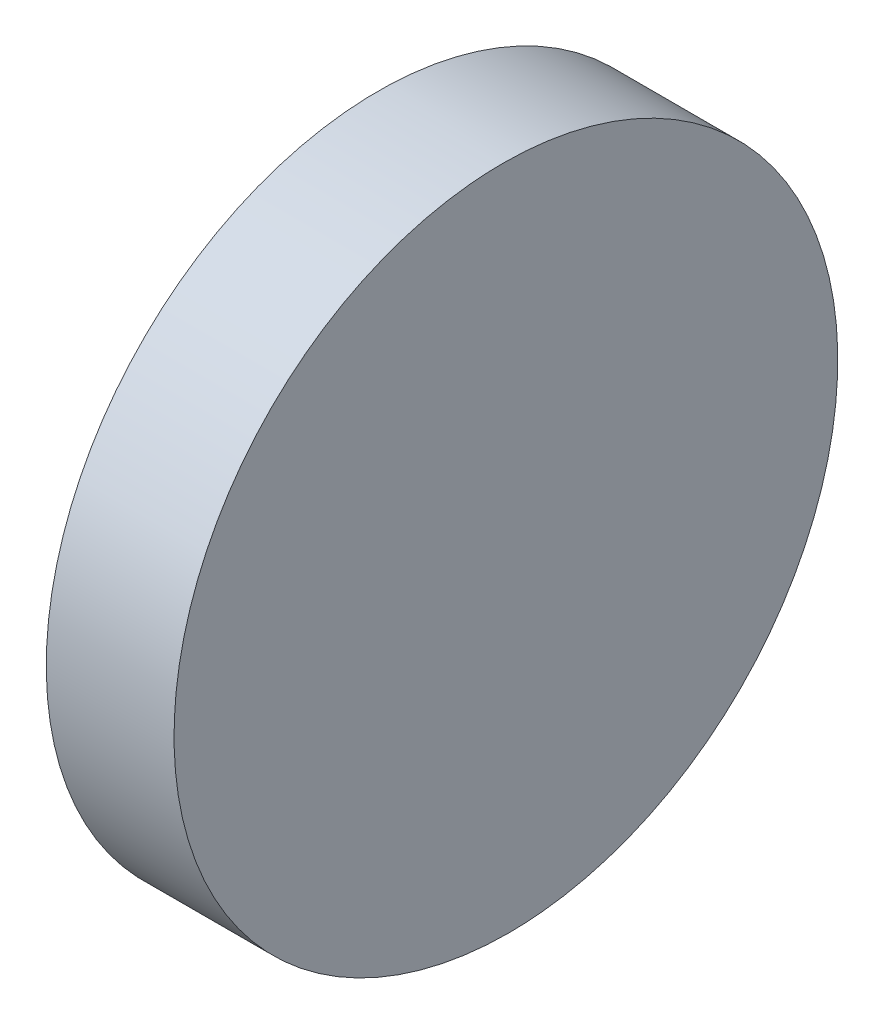
SolidWorks part; units mm, degrees
ref_plane "前视基准面" through (0, 0, 0) normal (0, 0, 1) x (1, 0, 0)
ref_plane "上视基准面" through (0, 0, 0) normal (0, 1, 0) x (1, 0, 0)
ref_plane "右视基准面" through (0, 0, 0) normal (1, 0, 0) x (0, 0, -1)
sketch "草图1" plane through (0, 0, 0) normal (0, 0, 1) x (1, 0, 0)
  line L0 (15.2768, 0) -> (-15.2768, 0) construction
  line L1 (0, 25.4) -> (0, -25.4)
  line L2 (0, -25.4) -> (10, -25.4)
  line L3 (10, -25.4) -> (9.5567, 25.4)
  line L4 (0, 25.4) -> (9.5567, 25.4)
  point P5 (0, 0)
  dimension "D1" = 10
  dimension "D2" = 50.8
  dimension "D3" = 0.5
extrude "凸台-拉伸1" add sketch "草图1" along normal blind 50.8 contours L1 L2 L3 L4
sketch "草图2" plane through (0, 0, 0) normal (-1, 0, 0) x (0, 0, 1)
  line L4 (0, 25.4) -> (0, -25.4)
  line L5 (0, -25.4) -> (50.8, -25.4)
  line L6 (50.8, -25.4) -> (50.8, 25.4)
  line L7 (50.8, 25.4) -> (0, 25.4)
  line L8 (0, 25.4) -> (0, -25.4)
  line L9 (0, -25.4) -> (50.8, -25.4)
  line L10 (50.8, -25.4) -> (50.8, 25.4)
  line L11 (50.8, 25.4) -> (0, 25.4)
  circle A0 centre (25.4, 0) radius 25.4
  point P7 (25.4, 25.4)
  line M1 (0, 25.4) -> (0, -25.4)
  line M2 (0, -25.4) -> (50.8, -25.4)
  line M3 (50.8, -25.4) -> (50.8, 25.4)
  line M4 (50.8, 25.4) -> (0, 25.4)
  dimension "D2" = 50.8
  dimension "D1" = 0
extrude "切除-拉伸1" cut sketch "草图2" against normal blind 10 contours A0 L8 M2 | A0 L9 M3 | A0 L10 M4 | A0 L11 M1
